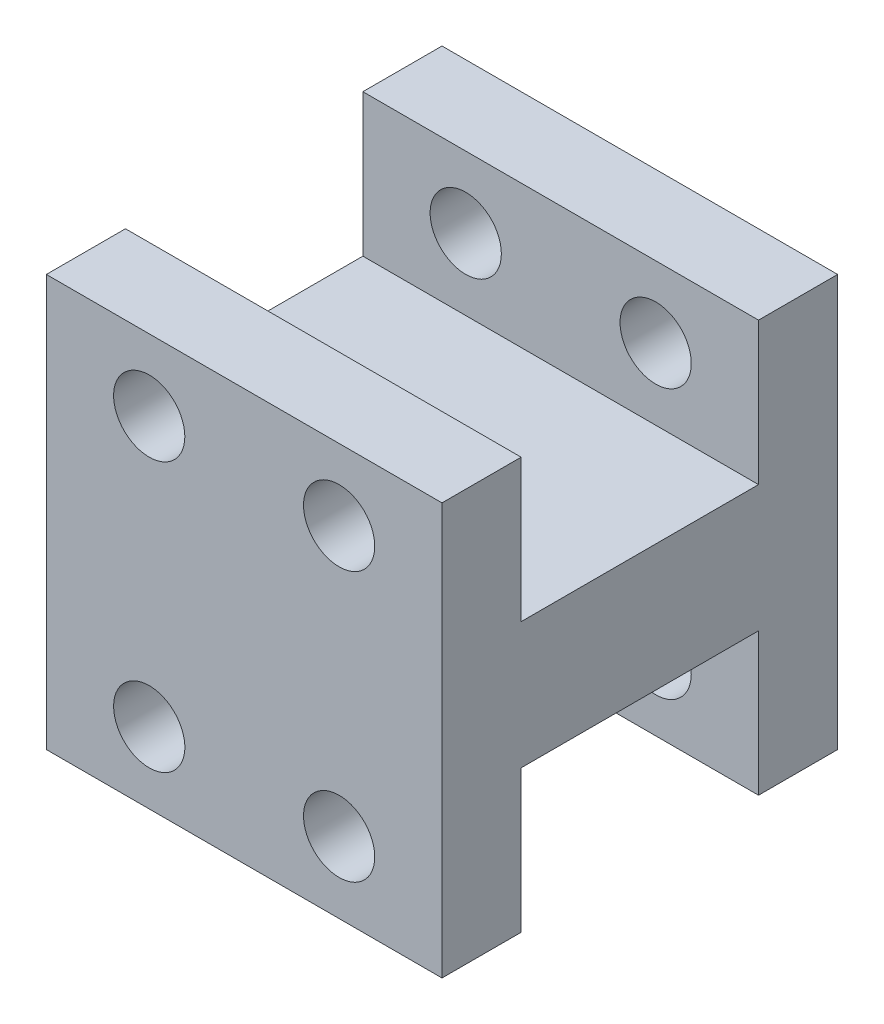
SolidWorks part; units mm, degrees
ref_plane "前视基准面" through (0, 0, 0) normal (0, 0, 1) x (1, 0, 0)
ref_plane "上视基准面" through (0, 0, 0) normal (0, 1, 0) x (1, 0, 0)
ref_plane "右视基准面" through (0, 0, 0) normal (1, 0, 0) x (0, 0, -1)
sketch "草图1" plane through (0, 0, 0) normal (0, 0, 1) x (1, 0, 0)
  line L1 (0, 0) -> (25, 0)
  line L2 (0, 0) -> (0, 50)
  line L3 (0, 50) -> (25, 50)
  line L4 (25, 0) -> (25, 50)
  dimension "D1" = 25
  dimension "D2" = 50
extrude "凸台-拉伸1" add sketch "草图1" along normal blind 5
sketch "草图2" plane through (0, 0, 5) normal (0, 0, 1) x (1, 0, 0)
  line L0 (12.5, 0) -> (12.5, 50) construction
  line L1 (0, 0) -> (25, 0) construction
  line L2 (25, 50) -> (0, 50) construction
  line L3 (12.5, 50) -> (12.5, 25) construction
  line L4 (12.5, 25) -> (-31.4554, 25) construction
  circle A0 centre (12.5, 7.5) radius 2.25
  circle A1 centre (12.5, 42.5) radius 2.25
  dimension "D1" = 4.5
  dimension "D2" = 35
extrude "切除-拉伸1" cut sketch "草图2" against normal blind 20
sketch "草图3" plane through (0, 0, 5) normal (0, 0, 1) x (1, 0, 0)
  line L0 (0, 25) -> (25, 25) construction
  line L1 (0, 50) -> (0, 0) construction
  line L2 (25, 0) -> (25, 50) construction
  line L4 (25, 21) -> (0, 21)
  line L5 (25, 21) -> (25, 29)
  line L6 (25, 29) -> (0, 29)
  line L7 (0, 21) -> (0, 29)
  dimension "D1" = 8
extrude "凸台-拉伸2" add sketch "草图3" along normal blind 15
sketch "草图4" plane through (0, 0, 20) normal (0, 0, 1) x (1, 0, 0)
  line L0 (0, 25) -> (25, 25) construction
  line L1 (0, 29) -> (0, 21) construction
  line L2 (25, 21) -> (25, 29) construction
  line L4 (25, 12) -> (0, 12)
  line L5 (25, 12) -> (25, 38)
  line L6 (25, 38) -> (0, 38)
  line L7 (0, 12) -> (0, 38)
  dimension "D1" = 26
extrude "凸台-拉伸3" add sketch "草图4" along normal blind 5
sketch "草图5" plane through (0, 0, 20) normal (0, 0, -1) x (-1, 0, 0)
  line L0 (-25, 33.5) -> (0, 33.5) construction
  line L1 (-25, 29) -> (-25, 38) construction
  line L2 (0, 38) -> (0, 29) construction
  line L3 (0, 33.5) -> (-12.5, 33.5) construction
  line L4 (-12.5, 38) -> (-12.5, 12) construction
  line L5 (-25, 38) -> (0, 38) construction
  line L6 (0, 12) -> (-25, 12) construction
  line L7 (-12.5, 12) -> (-12.5, 25) construction
  line L8 (-12.5, 25) -> (-19.4639, 25) construction
  circle A0 centre (-18.5, 33.5) radius 2.25
  circle A1 centre (-6.5, 33.5) radius 2.25
  circle A2 centre (-6.5, 16.5) radius 2.25
  circle A3 centre (-18.5, 16.5) radius 2.25
  dimension "D1" = 4.5
  dimension "D2" = 12
extrude "切除-拉伸2" cut sketch "草图5" against normal blind 5
sketch "草图6" plane through (0, 0, 0) normal (0, 0, -1) x (-1, 0, 0)
  line L1 (-25, 0) -> (0, 0)
  line L2 (-25, 0) -> (-25, 50)
  line L3 (-25, 50) -> (0, 50)
  line L4 (0, 0) -> (0, 50)
extrude "切除-拉伸3" cut sketch "草图6" against normal blind 5
ref_plane "基准面1" through (0, 0, 12.5) normal (0, 0, -1) x (-1, 0, 0)
mirror "镜向1" about plane through (0, 0, 12.5) normal (0, 0, -1) of "切除-拉伸2", "凸台-拉伸3"
